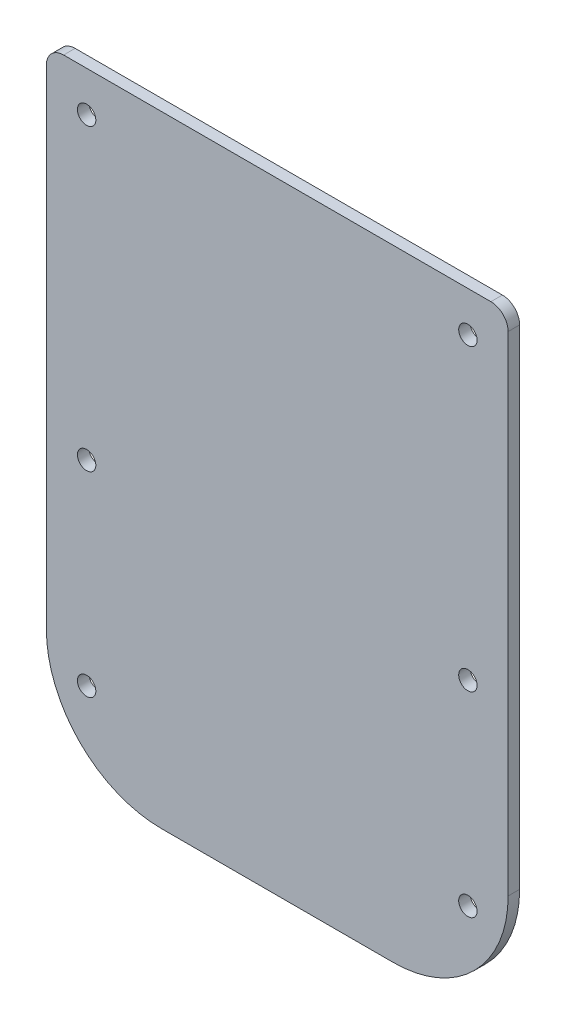
SolidWorks part; units mm, degrees
material "Acrylic (Medium-high impact)"
ref_plane "Front Plane" through (0, 0, 0) normal (0, 0, 1) x (1, 0, 0)
ref_plane "Top Plane" through (0, 0, 0) normal (0, 1, 0) x (1, 0, 0)
ref_plane "Right Plane" through (0, 0, 0) normal (1, 0, 0) x (0, 0, -1)
sketch "Sketch1" plane through (0, 0, 0) normal (0, 0, 1) x (1, 0, 0)
  line L1 (0, 0) -> (80.3, 0)
  line L2 (0, 0) -> (0, 66)
  line L3 (0, 66) -> (80.3, 66)
  line L4 (80.3, 0) -> (80.3, 66)
  dimension "D1" = 80.3
  dimension "D2" = 66
extrude "Boss-Extrude1" add sketch "Sketch1" along normal blind 2
hole_wizard "Ø3.2 (3.2) Diameter Hole1" positions "Sketch3" profile "Sketch2" hole size "Ø3.2" standard "ANSI Metric" end condition through all
sketch "Sketch3" plane through (0, 0, 2) normal (0, 0, 1) x (1, 0, 0)
  line L0 (0, 33) -> (80.3, 33) construction
  line L1 (0, 66) -> (0, 0) construction
  line L2 (80.3, 0) -> (80.3, 66) construction
  line L4 (7, 7) -> (7, 59) construction
  line L6 (7, 59) -> (73.3, 59) construction
  line L7 (73.3, 59) -> (73.3, 7) construction
  line L8 (73.3, 7) -> (7, 7) construction
  line L10 (40.15, 66) -> (40.15, 0) construction
  line L11 (80.3, 66) -> (0, 66) construction
  line L12 (0, 0) -> (80.3, 0) construction
  point P0 (7, 59)
  point P2 (73.3, 59)
  point P4 (73.3, 7)
  point P6 (7, 7)
  dimension "D1" = 66.3
  dimension "D2" = 52
  dimension "D3" = 26
  dimension "D4" = 33.15
sketch "Sketch2" plane through (7, 59, 2) normal (1, 0, 0) x (0, -1, 0)
  line L0 (0, 0) -> (0, 2)
  line L1 (0, 2) -> (1.6, 2)
  line L2 (1.6, 2) -> (1.6, 0)
  line L5 (1.6, 0) -> (0, 0)
  line L11 (0, -6.35) -> (0, 107.95) construction
  dimension "Thru Hole Dia." = 3.2
  dimension "Thru Hole Depth" = 2
fillet "Fillet1" radius 3 2 edges at (80.3, 66, 1) (0, 66, 1)
sketch "Sketch4" plane through (0, 0, 0) normal (0, -1, 0) x (1, 0, 0)
  line L4 (0, 0) -> (80.3, 0)
  line L5 (80.3, 0) -> (80.3, 2)
  line L6 (80.3, 2) -> (0, 2)
  line L7 (0, 2) -> (0, 0)
  line L8 (0, 0) -> (80.3, 0)
  line L9 (80.3, 0) -> (80.3, 2)
  line L10 (80.3, 2) -> (0, 2)
  line L11 (0, 2) -> (0, 0)
  dimension "D1" = 0
extrude "Boss-Extrude2" add sketch "Sketch4" along normal blind 42
fillet "Fillet2" radius 20 2 edges at (0, -42, 1) (80.3, -42, 1)
hole_wizard "Ø3.2 (3.2) Diameter Hole2" positions "Sketch6" profile "Sketch5" hole size "Ø3.2" standard "ANSI Metric"
sketch "Sketch6" plane through (0, 0, 2) normal (0, 0, 1) x (1, 0, 0)
  line L0 (7, -27) -> (73.3, -27) construction
  line L2 (40.15, -42) -> (40.15, 66) construction
  line L3 (60.3, -42) -> (20, -42) construction
  line L4 (77.3, 66) -> (3, 66) construction
  line L5 (40.15, -27) -> (40.15, -42) construction
  line L10 (0, 63) -> (0, -22) construction
  point P0 (7, -27)
  point P2 (73.3, -27)
  dimension "D2" = 7
  dimension "D1" = 15
sketch "Sketch5" plane through (7, -27, 2) normal (1, 0, 0) x (0, -1, 0)
  line L0 (0, 0) -> (0, 60.9614)
  line L1 (0, 60.9614) -> (1.6, 60)
  line L2 (1.6, 60) -> (1.6, 0)
  line L5 (1.6, 0) -> (0, 0)
  line L10 (0, 60.9614) -> (-1.6, 60) construction
  line L11 (0, -6.35) -> (0, 107.95) construction
  dimension "Hole Dia." = 3.2
  dimension "Hole Depth" = 60
  dimension "Drill Angle" = 118
